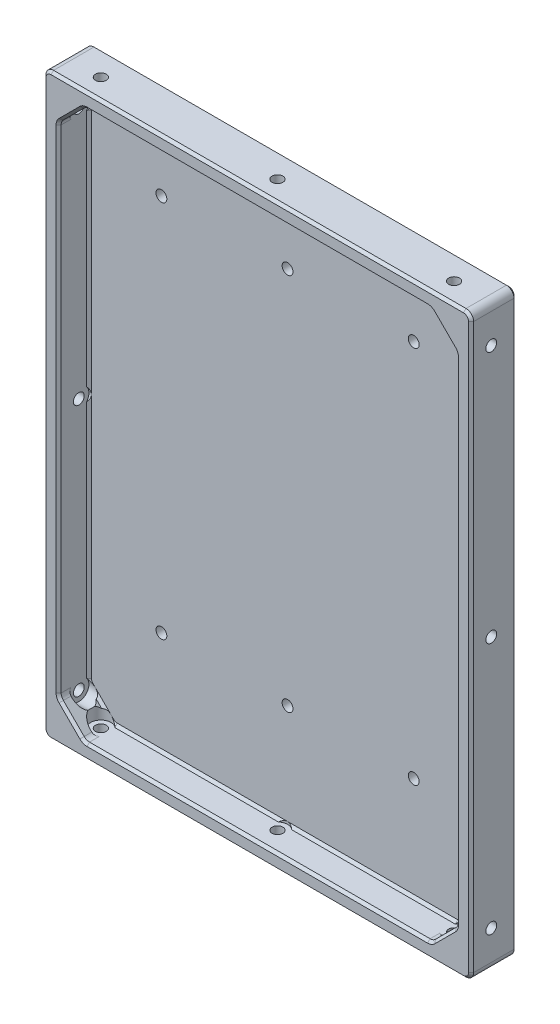
SolidWorks part; units mm, degrees
ref_plane "正面" through (0, 0, 0) normal (0, 0, 1) x (1, 0, 0)
ref_plane "平面" through (0, 0, 0) normal (0, 1, 0) x (1, 0, 0)
ref_plane "右側面" through (0, 0, 0) normal (1, 0, 0) x (0, 0, -1)
sketch "ｽｹｯﾁ1" plane through (0, 0, 0) normal (0, 0, 1) x (1, 0, 0)
  line L1 (84.75, -114.75) -> (-84.75, -114.75)
  line L2 (84.75, -114.75) -> (84.75, 114.75)
  line L3 (84.75, 114.75) -> (-84.75, 114.75)
  line L4 (-84.75, -114.75) -> (-84.75, 114.75)
  line L5 (84.75, -114.75) -> (-84.75, 114.75) construction
  line L6 (84.75, 114.75) -> (-84.75, -114.75) construction
  point P0 (0, 0)
  dimension "D1" = 229.5
  dimension "D2" = 169.5
extrude "ﾎﾞｽ - 押し出し1" add sketch "ｽｹｯﾁ1" along normal blind 6
sketch "ｽｹｯﾁ2" plane through (0, 0, 6) normal (0, 0, 1) x (1, 0, 0)
  line L1 (78.75, -108.75) -> (-78.75, -108.75)
  line L2 (78.75, -108.75) -> (78.75, 108.75)
  line L3 (78.75, 108.75) -> (-78.75, 108.75)
  line L4 (-84.75, 114.75) -> (-84.75, -114.75)
  line L5 (-84.75, -114.75) -> (84.75, -114.75)
  line L6 (84.75, -114.75) -> (84.75, 114.75)
  line L7 (84.75, 114.75) -> (-84.75, 114.75)
  line L8 (-84.75, 114.75) -> (-84.75, -114.75)
  line L9 (-84.75, -114.75) -> (84.75, -114.75)
  line L10 (84.75, -114.75) -> (84.75, 114.75)
  line L11 (84.75, 114.75) -> (-84.75, 114.75)
  line L12 (-78.75, -108.75) -> (-78.75, 108.75)
  line L13 (78.75, -108.75) -> (-78.75, 108.75) construction
  line L14 (78.75, 108.75) -> (-78.75, -108.75) construction
  point P2 (0, 0)
  dimension "D2" = 6
  dimension "D3" = 6
  dimension "D1" = 0
extrude "ﾎﾞｽ - 押し出し2" add sketch "ｽｹｯﾁ2" along normal blind 12
chamfer "面取り1" distance 10 angle 45 4 edges at (-78.75, -108.75, 12) (78.75, -108.75, 12) (78.75, 108.75, 12) (-78.75, 108.75, 12)
fillet "ﾌｨﾚｯﾄ1" radius 3 8 edges at (68.75, 108.75, 12) (78.75, 98.75, 12) (-68.75, 108.75, 12) (-78.75, 98.75, 12) (-78.75, -98.75, 12) (-68.75, -108.75, 12) (68.75, -108.75, 12) (78.75, -98.75, 12)
chamfer "面取り2" distance 1 angle 45 32 edges at (78.75, 0, 18) (78.5216, 98.6554, 18) (78.5216, -98.6554, 18) (73.75, 103.75, 18) (73.75, -103.75, 18) (68.6554, 108.5216, 18) (68.6554, -108.5216, 18) (0, 108.75, 18) (0, -108.75, 18) (-68.6554, 108.5216, 18) (-68.6554, -108.5216, 18) (-73.75, 103.75, 18) (-73.75, -103.75, 18) (-78.5216, 98.6554, 18) (-78.5216, -98.6554, 18) (-78.75, 0, 18) (78.75, 0, 6) (78.5216, 98.6554, 6) (78.5216, -98.6554, 6) (73.75, 103.75, 6) (73.75, -103.75, 6) (68.6554, 108.5216, 6) (68.6554, -108.5216, 6) (0, 108.75, 6) (0, -108.75, 6) (-68.6554, 108.5216, 6) (-68.6554, -108.5216, 6) (-73.75, 103.75, 6) (-73.75, -103.75, 6) (-78.5216, 98.6554, 6) (-78.5216, -98.6554, 6) (-78.75, 0, 6)
fillet "ﾌｨﾚｯﾄ2" radius 3 4 edges at (84.75, 114.75, 9) (-84.75, 114.75, 9) (84.75, -114.75, 9) (-84.75, -114.75, 9)
chamfer "面取り3" distance 1 angle 45 16 edges at (-84.75, 0, 18) (-83.8713, -113.8713, 18) (-83.8713, 113.8713, 18) (0, -114.75, 18) (0, 114.75, 18) (83.8713, -113.8713, 18) (83.8713, 113.8713, 18) (84.75, 0, 18) (-84.75, 0, 0) (-83.8713, -113.8713, 0) (-83.8713, 113.8713, 0) (0, -114.75, 0) (0, 114.75, 0) (83.8713, -113.8713, 0) (83.8713, 113.8713, 0) (84.75, 0, 0)
ref_plane "平面1" through (-68.75, 0, 0) normal (1, 0, 0) x (0, 0, -1)
sketch "ｽｹｯﾁ4" plane through (-68.75, 0, 0) normal (1, 0, 0) x (0, 0, -1)
  line L0 (-10, 100) -> (-10, -100)
  dimension "D1" = 10
  dimension "D2" = 200
  dimension "D3" = 100
hole_wizard "M4 六角穴付き頭ねじ用座ぐり穴1" positions "ｽｹｯﾁ5" profile "ｽｹｯﾁ7" counterbore size "M4" standard "ISO"
sketch "ｽｹｯﾁ5" plane through (-68.75, 0, 0) normal (1, 0, 0) x (0, 0, -1)
  line L0 (-10, 100) -> (-10, -100) construction
  point P0 (-10, 0)
  point P4 (-10, 100)
  point P7 (-10, -100)
sketch "ｽｹｯﾁ7" plane through (-68.75, 0, 10) normal (0, 1, 0) x (0, 0, -1)
  line L0 (0, 0) -> (0, 16)
  line L1 (0, 16) -> (2.15, 16)
  line L3 (2.15, 16) -> (2.15, 10)
  line L4 (2.15, 10) -> (4, 10)
  line L5 (4, 10) -> (4, 0)
  line L7 (4, 0) -> (0, 0)
  line L11 (0, -6.35) -> (0, 107.95) construction
  dimension "通し穴の直径" = 4.3
  dimension "通し穴の深さ" = 16
  dimension "座ぐり穴の直径" = 8
  dimension "座ぐり穴の深さ" = 10
mirror "ﾐﾗｰ1" about plane through (0, 0, 0) normal (1, 0, 0) of "M4 六角穴付き頭ねじ用座ぐり穴1"
ref_plane "平面2" through (0, 98.75, 0) normal (0, -1, 0) x (-1, 0, 0)
sketch "ｽｹｯﾁ8" plane through (0, 98.75, 0) normal (0, -1, 0) x (-1, 0, 0)
  line L0 (-70, -10) -> (70, -10)
  line L1 (-81.75, 0) -> (81.75, 0) construction
  dimension "D1" = 10
  dimension "D2" = 140
  dimension "D3" = 70
hole_wizard "M4 六角穴付き頭ねじ用座ぐり穴2" positions "ｽｹｯﾁ9" profile "ｽｹｯﾁ10" counterbore size "M4" standard "ISO"
sketch "ｽｹｯﾁ9" plane through (0, 98.75, 0) normal (0, -1, 0) x (-1, 0, 0)
  point P0 (-70, -10)
  point P3 (70, -10)
  point P6 (0, -10)
sketch "ｽｹｯﾁ10" plane through (70, 98.75, 10) normal (1, 0, 0) x (0, 0, -1)
  line L0 (0, 0) -> (0, 16)
  line L1 (0, 16) -> (2.15, 16)
  line L3 (2.15, 16) -> (2.15, 10)
  line L4 (2.15, 10) -> (4, 10)
  line L5 (4, 10) -> (4, 0)
  line L7 (4, 0) -> (0, 0)
  line L11 (0, -6.35) -> (0, 107.95) construction
  dimension "通し穴の直径" = 4.3
  dimension "通し穴の深さ" = 16
  dimension "座ぐり穴の直径" = 8
  dimension "座ぐり穴の深さ" = 10
mirror "ﾐﾗｰ2" about plane through (0, 0, 0) normal (0, 1, 0) of "M4 六角穴付き頭ねじ用座ぐり穴2"
sketch "ｽｹｯﾁ11" plane through (0, 0, 6) normal (0, 0, 1) x (1, 0, 0)
  line L1 (50, -68) -> (0, -68)
  line L2 (50, -68) -> (50, 82)
  line L3 (50, 82) -> (0, 82)
  line L4 (0, -68) -> (0, 82)
  line L5 (50, -68) -> (0, 82) construction
  line L6 (50, 82) -> (0, -68) construction
  line L7 (0, 82) -> (-50, 82)
  line L8 (0, 82) -> (0, -68)
  line L9 (0, -68) -> (-50, -68)
  line L10 (-50, 82) -> (-50, -68)
  point P0 (0, 0)
  point P9 (25, 7)
  dimension "D1" = 150
  dimension "D2" = 50
  dimension "D3" = 7
  dimension "D4" = 25
  dimension "D5" = 50
hole_wizard "M4 すきま穴1" positions "ｽｹｯﾁ12" profile "ｽｹｯﾁ14" hole size "M4" standard "ISO" end condition through all
sketch "ｽｹｯﾁ12" plane through (0, 0, 6) normal (0, 0, 1) x (1, 0, 0)
  point P0 (0, 82)
  point P3 (50, 82)
  point P6 (50, -68)
  point P9 (0, -68)
  point P12 (-50, 82)
  point P15 (-50, -68)
sketch "ｽｹｯﾁ14" plane through (0, 82, 6) normal (1, 0, 0) x (0, -1, 0)
  line L0 (0, 0) -> (0, 6)
  line L1 (0, 6) -> (2.15, 6)
  line L2 (2.15, 6) -> (2.15, 0)
  line L5 (2.15, 0) -> (0, 0)
  line L11 (0, -6.35) -> (0, 107.95) construction
  dimension "通し穴の直径" = 4.3
  dimension "通し穴の深さ" = 6
